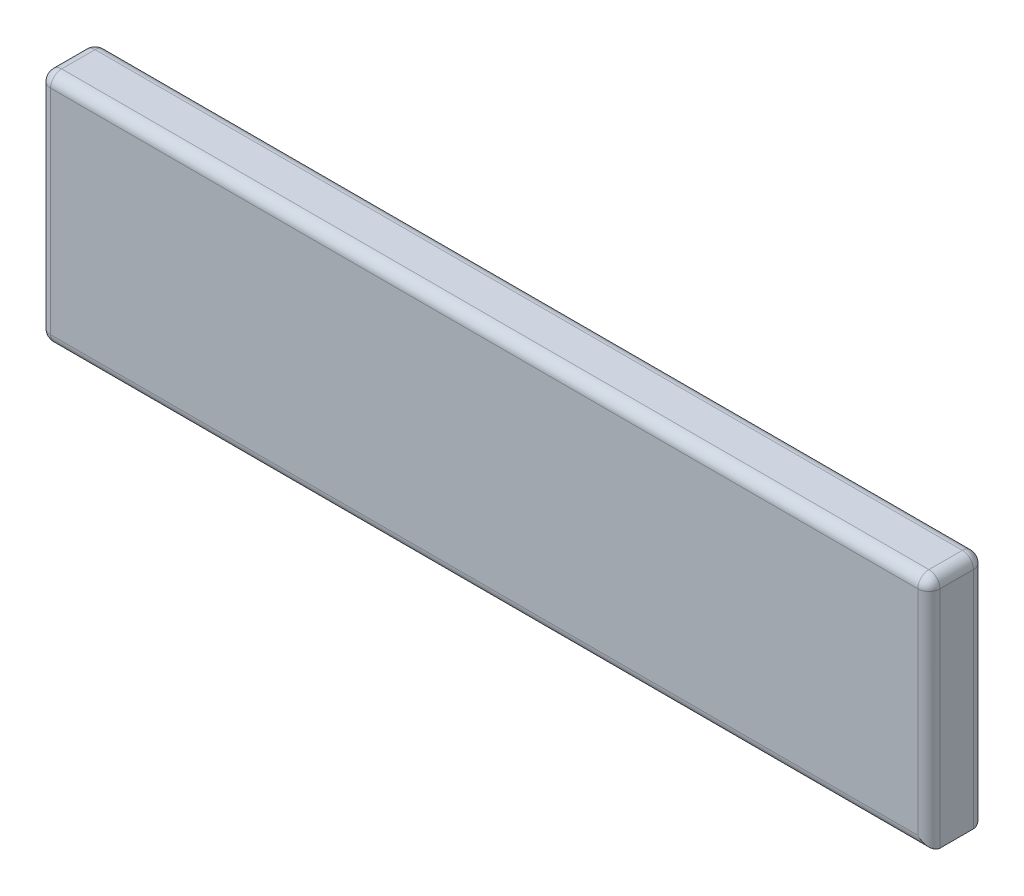
SolidWorks part; units mm, degrees
ref_plane "Front Plane" through (0, 0, 0) normal (0, 0, 1) x (1, 0, 0)
ref_plane "Top Plane" through (0, 0, 0) normal (0, 1, 0) x (1, 0, 0)
ref_plane "Right Plane" through (0, 0, 0) normal (1, 0, 0) x (0, 0, -1)
sketch "Sketch1" plane through (0, 0, 0) normal (0, 0, 1) x (1, 0, 0)
  line L1 (-26.6964, -2.4952) -> (13.3036, -2.4952)
  line L2 (-26.6964, -2.4952) -> (-26.6964, -13.0952)
  line L3 (-26.6964, -13.0952) -> (13.3036, -13.0952)
  line L4 (13.3036, -2.4952) -> (13.3036, -13.0952)
  dimension "D1" = 40
  dimension "D2" = 10.6
extrude "Boss-Extrude1" add sketch "Sketch1" along normal blind 2.5
fillet "Fillet1" radius 0.5 11 edges at (-26.6964, -13.0952, 1.25) (-6.6964, -13.0952, 0) (13.3036, -7.7952, 0) (-26.6964, -7.7952, 0) (13.3036, -7.7952, 2.5) (-6.6964, -13.0952, 2.5) (-26.6964, -7.7952, 2.5) (13.3036, -2.4952, 1.25) (-6.6964, -2.4952, 2.5) (-26.6964, -2.4952, 1.25) (-6.6964, -2.4952, 0)
